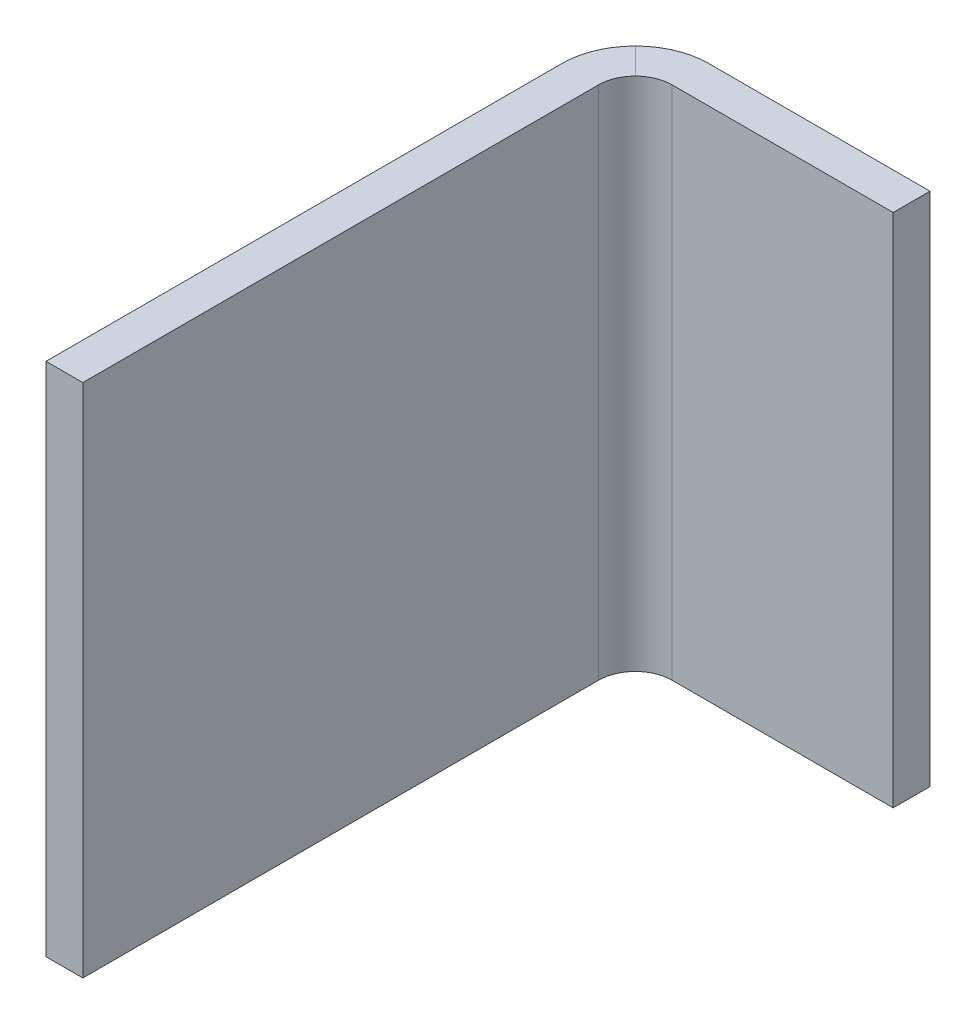
SolidWorks part; units mm, degrees
ref_plane "Front Plane" through (0, 0, 0) normal (0, 0, 1) x (1, 0, 0)
ref_plane "Top Plane" through (0, 0, 0) normal (0, 1, 0) x (1, 0, 0)
ref_plane "Right Plane" through (0, 0, 0) normal (1, 0, 0) x (0, 0, -1)
sketch "Sketch1" plane through (0, 0, 0) normal (0, 0, 1) x (1, 0, 0)
  line L0 (0, 22.225) -> (0, -22.225)
  line L1 (0, 0) -> (3.175, 0)
  point P4 (0, 0)
  point P8 (0, 0)
  point P9 (0, 0)
sketch "Sketch2" plane through (0, 0, 0) normal (0, 1, 0) x (1, 0, 0)
  line L0 (0, 0) -> (0, 47.625)
  line L1 (3.175, 50.8) -> (25.4, 50.8)
  arc A0 (3.175, 50.8) -> (0, 47.625) centre (3.175, 47.625) ccw
  point P6 (0, 50.8)
sketch "Sketch3" plane through (0, 0, 0) normal (0, 0, 1) x (1, 0, 0)
  line L8 (3.175, -22.225) -> (0, -22.225)
  line L9 (3.175, -22.225) -> (3.175, 22.225)
  line L10 (0, -22.225) -> (0, 22.225)
  line L11 (3.175, 22.225) -> (0, 22.225)
  line L12 (3.175, -22.225) -> (0, 22.225) construction
  line L13 (0, -22.225) -> (3.175, 22.225) construction
  line L14 (0, 0) -> (3.175, 0) construction
  point P1 (0, 0)
  point P2 (1.5875, 0)
  dimension "D1" = 3.175
  dimension "D2" = 44.45
  dimension "D3" = 22.225
sketch "Sketch4" plane through (0, 0, 0) normal (0, 1, 0) x (1, 0, 0)
  line L0 (0, 0) -> (0, 50.8)
  line L1 (0, 50.8) -> (25.4, 50.8)
  dimension "D1" = 50.8
  dimension "D2" = 25.4
sweep "Sweep1" add profiles "Sketch3" path "Sketch4"
fillet "Fillet1" radius 3.175 1 edges at (3.175, 0, -47.625)
fillet "Fillet2" radius 6.35 1 edges at (0, 0, -50.8)
equation "\"D1@Sketch3\"=\"Thickness@Sketch1\""
equation "\"D2@Sketch3\"=\"LengthC@Sketch1\""
equation "\"D3@Sketch3\"=\"LengthC@Sketch1\"/2"
equation "\"D1@Sketch4\"=\"LengthA@Sketch2\""
equation "\"D2@Sketch4\"=\"LengthB@Sketch2\""
equation "\"D1@Fillet1\"=\"CornerRadius@Sketch2\""
equation "\"D1@Fillet2\"=\"CornerRadius@Sketch2\"*2"
